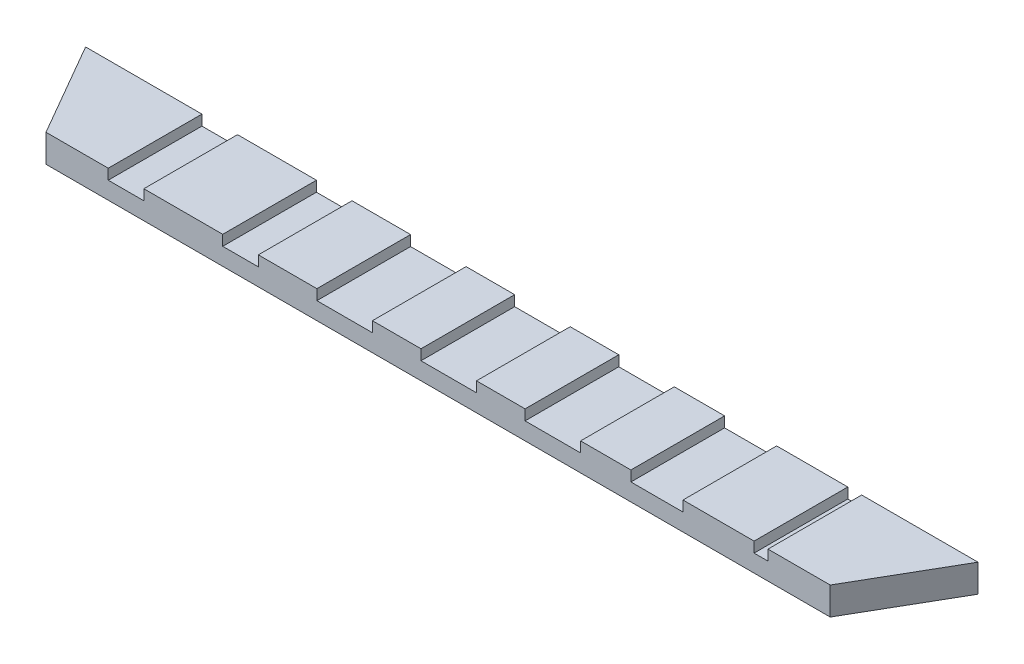
SolidWorks part; units mm, degrees
ref_plane "Front Plane" through (0, 0, 0) normal (0, 0, 1) x (1, 0, 0)
ref_plane "Top Plane" through (0, 0, 0) normal (0, 1, 0) x (1, 0, 0)
ref_plane "Right Plane" through (0, 0, 0) normal (1, 0, 0) x (0, 0, -1)
sketch "Sketch1" plane through (0, 0, 0) normal (0, 1, 0) x (1, 0, 0)
  line L1 (-113, -12.6289) -> (113, -12.6289)
  line L2 (-113, -12.6289) -> (-128.5885, 14.3711)
  line L3 (-128.5885, 14.3711) -> (128.5885, 14.3711)
  line L4 (113, -12.6289) -> (128.5885, 14.3711)
  line L5 (-113, -12.6289) -> (128.5885, 14.3711) construction
  line L6 (-128.5885, 14.3711) -> (113, -12.6289) construction
  point P0 (0, 0)
  dimension "D1" = 226
  dimension "D2" = 27
  dimension "D3" = 120
extrude "Boss-Extrude1" add sketch "Sketch1" along normal blind 8
sketch "Sketch4" plane through (0, 8, 0) normal (0, 1, 0) x (1, 0, 0)
  line L0 (-120.7942, 0.8711) -> (120.7942, 0.8711) construction
  line L1 (-62.0646, 14.3711) -> (-62.0646, -12.6289)
  line L2 (-62.0646, -12.6289) -> (-51.8063, -12.6289)
  line L3 (-51.8063, 14.3711) -> (-51.8063, -12.6289)
  line L4 (-62.0646, 14.3711) -> (-51.8063, -12.6289) construction
  line L9 (-128.5885, 14.3711) -> (-113, -12.6289) construction
  line L10 (113, -12.6289) -> (128.5885, 14.3711) construction
  line L11 (-113, -12.6289) -> (113, -12.6289) construction
  line L16 (-95.0646, 14.3711) -> (-84.8063, 14.3711)
  line L17 (-95.0646, 14.3711) -> (-95.0646, -12.6289)
  line L22 (-95.0646, -12.6289) -> (-84.8063, -12.6289)
  line L23 (-84.8063, 14.3711) -> (-84.8063, -12.6289)
  line L28 (-95.0646, 14.3711) -> (-84.8063, -12.6289) construction
  line L29 (-95.0646, -12.6289) -> (-84.8063, 14.3711) construction
  line L30 (-62.0646, -12.6289) -> (-51.8063, 14.3711) construction
  line L31 (-62.0646, 14.3711) -> (-51.8063, 14.3711)
  line L35 (128.5885, 14.3711) -> (-128.5885, 14.3711) construction
  line L41 (-34.9354, -12.6289) -> (-18.9354, -12.6289)
  line L47 (-34.9354, -12.6289) -> (-34.9354, 14.3711)
  line L53 (-34.9354, 14.3711) -> (-18.9354, 14.3711)
  line L59 (-18.9354, -12.6289) -> (-18.9354, 14.3711)
  line L70 (-34.9354, -12.6289) -> (-18.9354, 14.3711) construction
  line L71 (-34.9354, 14.3711) -> (-18.9354, -12.6289) construction
  line L73 (-4.9354, -12.6289) -> (11.0646, -12.6289)
  line L74 (-4.9354, -12.6289) -> (-4.9354, 14.3711)
  line L75 (-4.9354, 14.3711) -> (11.0646, 14.3711)
  line L76 (11.0646, -12.6289) -> (11.0646, 14.3711)
  line L77 (-4.9354, -12.6289) -> (11.0646, 14.3711) construction
  line L78 (-4.9354, 14.3711) -> (11.0646, -12.6289) construction
  line L80 (25.0646, -12.6289) -> (41.0646, -12.6289)
  line L81 (25.0646, -12.6289) -> (25.0646, 14.3711)
  line L82 (25.0646, 14.3711) -> (41.0646, 14.3711)
  line L83 (41.0646, -12.6289) -> (41.0646, 14.3711)
  line L84 (25.0646, -12.6289) -> (41.0646, 14.3711) construction
  line L85 (25.0646, 14.3711) -> (41.0646, -12.6289) construction
  line L87 (55.5646, -12.6289) -> (70.5646, -12.6289)
  line L88 (55.5646, -12.6289) -> (55.5646, 14.3711)
  line L89 (55.5646, 14.3711) -> (70.5646, 14.3711)
  line L90 (70.5646, -12.6289) -> (70.5646, 14.3711)
  line L91 (55.5646, -12.6289) -> (70.5646, 14.3711) construction
  line L92 (55.5646, 14.3711) -> (70.5646, -12.6289) construction
  line L93 (-95.0646, -12.6289) -> (95.0646, 14.3711) construction
  line L94 (91.0646, -12.6289) -> (95.0646, -12.6289)
  line L95 (91.0646, -12.6289) -> (91.0646, 14.3711)
  line L96 (91.0646, 14.3711) -> (95.0646, 14.3711)
  line L97 (95.0646, -12.6289) -> (95.0646, 14.3711)
  line L98 (91.0646, -12.6289) -> (95.0646, 14.3711) construction
  line L99 (91.0646, 14.3711) -> (95.0646, -12.6289) construction
  point P2 (-26.9354, 0.8711)
  point P7 (-89.9354, 0.8711)
  point P14 (108.8146, 0.8711)
  point P25 (3.0646, 0.8711)
  point P30 (33.0646, 0.8711)
  point P35 (63.0646, 0.8711)
  point P42 (93.0646, 0.8711)
  point P47 (-56.9354, 14.3711)
  point P49 (-26.9354, 14.3711)
  point P50 (0, 0.8711)
  dimension "D1" = 10.2582
  dimension "D3" = 16
  dimension "D4" = 16
  dimension "D5" = 16
  dimension "D6" = 15
  dimension "D7" = 4
  dimension "D8" = 30
  dimension "D9" = 30
  dimension "D10" = 30
  dimension "D11" = 30
  dimension "D12" = 30
  dimension "D2" = 2
extrude "Cut-Extrude1" cut sketch "Sketch4" against normal blind 3
equation "\"FullCut\"= 8"
equation "\"FullSpacing\"= 33"
equation "\"CornersHeight\"= 15"
equation "\"EdgesHeight\"= 16"
equation "\"FullSingle\"= 4"
equation "\"FullSingleSpacing\"= 16.5"
equation "\"D3@Sketch4\"=\"EdgesHeight\""
equation "\"D4@Sketch4\"=\"EdgesHeight\""
equation "\"D5@Sketch4\"=\"EdgesHeight\""
equation "\"D6@Sketch4\"=\"CornersHeight\""
equation "\"D7@Sketch4\"=\"FullSingle\""
